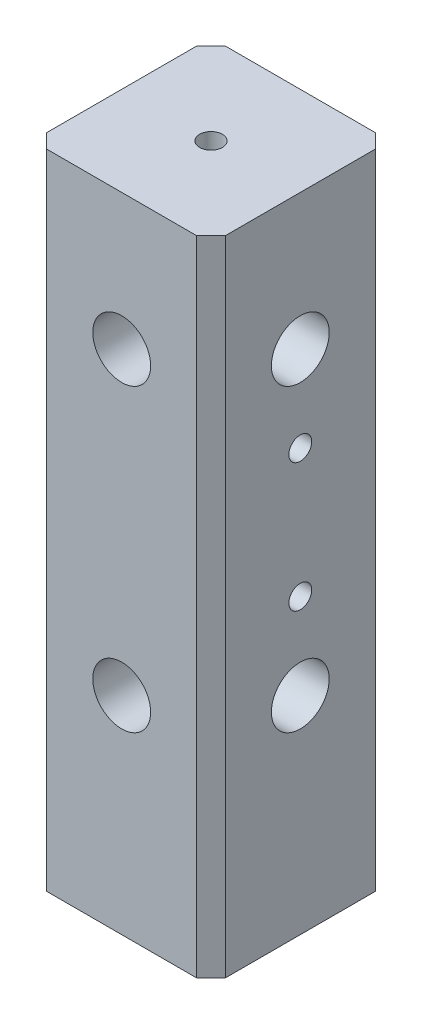
SolidWorks part; units mm, degrees
ref_plane "Front Plane" through (0, 0, 0) normal (0, 0, 1) x (1, 0, 0)
ref_plane "Top Plane" through (0, 0, 0) normal (0, 1, 0) x (1, 0, 0)
ref_plane "Right Plane" through (0, 0, 0) normal (1, 0, 0) x (0, 0, -1)
sketch "Sketch1" plane through (0, 0, 0) normal (0, 1, 0) x (1, 0, 0)
  line L1 (12.5, 12.5) -> (-12.5, 12.5)
  line L2 (12.5, 12.5) -> (12.5, -12.5)
  line L3 (12.5, -12.5) -> (-12.5, -12.5)
  line L4 (-12.5, 12.5) -> (-12.5, -12.5)
  point P4 (0, 12.5)
  point P6 (12.5, 0)
  dimension "D1" = 25
  dimension "D2" = 25
extrude "Boss-Extrude1" add sketch "Sketch1" along normal blind 90
sketch "Sketch2" plane through (12.5, 0, 0) normal (1, 0, 0) x (0, 0, -1)
  line L0 (-12.5, 90) -> (12.5, 90) construction
  line L3 (12.5, 90) -> (12.5, 0) construction
  circle A0 centre (0, 71) radius 4.05
  circle A1 centre (0, 29) radius 4.05
  dimension "D1" = 12.5
  dimension "D3" = 42
  dimension "D4" = 19
  dimension "D5" = 12.5
extrude "Cut-Extrude1" cut sketch "Sketch2" against normal blind 8 contours A1 | A0
sketch "Sketch3" plane through (0, 0, 12.5) normal (0, 0, 1) x (1, 0, 0)
  line L0 (-12.5, 90) -> (12.5, 90) construction
  line L2 (12.5, 90) -> (12.5, 0) construction
  circle A0 centre (0, 29) radius 4.05
  circle A1 centre (0, 71) radius 4.05
  dimension "D1" = 19
  dimension "D2" = 42
  dimension "D3" = 12.5
  dimension "D4" = 12.5
extrude "Cut-Extrude7" cut sketch "Sketch3" against normal blind 8 contours A0 | A1
chamfer "Chamfer1" distance 2 angle 45 1 edges at (12.5, 45, 12.5)
sketch "Sketch4" plane through (0, 90, 0) normal (0, 1, 0) x (1, 0, 0)
sketch "Sketch5" plane through (12.5, 0, 0) normal (1, 0, 0) x (0, 0, -1)
  circle A0 centre (0, 59) radius 1.6
  circle A1 centre (0, 41) radius 1.6
  circle A2 centre (0, 71) radius 4.05 construction
  circle A3 centre (0, 29) radius 4.05 construction
  dimension "D1" = 12
  dimension "D2" = 12
extrude "Cut-Extrude8" cut sketch "Sketch5" against normal blind 12.5
sketch "Sketch7" plane through (0, 90, 0) normal (0, 1, 0) x (1, 0, 0)
  circle A0 centre (0, 0) radius 1.6
extrude "Cut-Extrude9" cut sketch "Sketch7" against normal blind 10
